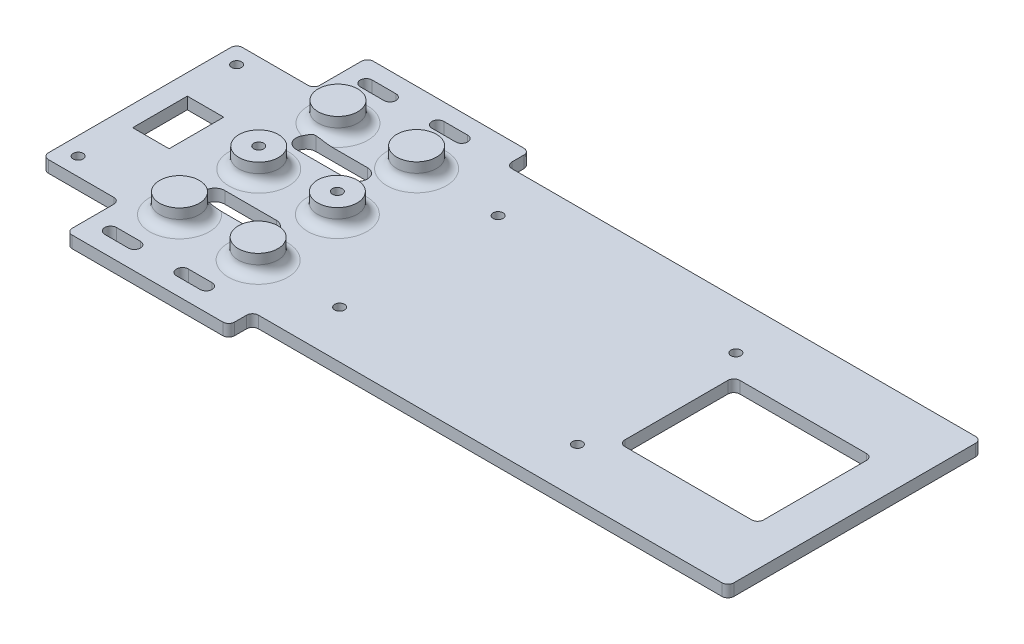
SolidWorks part; units mm, degrees
ref_plane "Front Plane" through (0, 0, 0) normal (0, 0, 1) x (1, 0, 0)
ref_plane "Top Plane" through (0, 0, 0) normal (0, 1, 0) x (1, 0, 0)
ref_plane "Right Plane" through (0, 0, 0) normal (1, 0, 0) x (0, 0, -1)
sketch "Sketch1" plane through (0, 0, 0) normal (0, 1, 0) x (1, 0, 0)
  line L1 (-20.5, -38) -> (20.5, -38)
  line L2 (20.5, -38) -> (20.5, -32)
  line L3 (20.5, -32) -> (140.5, -32)
  line L4 (140.5, -32) -> (140.5, 32)
  line L5 (140.5, 32) -> (20.5, 32)
  line L6 (20.5, 32) -> (20.5, 38)
  line L7 (20.5, 38) -> (-20.5, 38)
  line L8 (-20.5, -24.5) -> (-20.5, -38)
  line L21 (-20.5, 24.5) -> (-20.5, 38)
  line L24 (-40, 24.5) -> (-20.5, 24.5)
  line L26 (-40, 24.5) -> (-40, -24.5)
  line L27 (-40, -24.5) -> (-20.5, -24.5)
  line L28 (-35.5, -20) -> (-35.5, 20) construction
  line L29 (-31, -24.5) -> (-31, 24.5) construction
  circle A0 centre (-35.5, 20) radius 1.25
  circle A1 centre (-35.5, -20) radius 1.25
  point P2 (0, 38)
  point P3 (-40, 0)
  point P22 (-35.5, 0)
  dimension "D7" = 4.5
  dimension "D5" = 4.5
  dimension "D10" = 2.5
  dimension "D1" = 41
  dimension "D2" = 120
  dimension "D3" = 64
  dimension "D4" = 76
  dimension "D6" = 40
  dimension "D8" = 9
  dimension "D9" = 10.5
extrude "Boss-Extrude1" add sketch "Sketch1" along normal blind 3
sketch "Sketch2" plane through (0, 3, 0) normal (0, 1, 0) x (1, 0, 0)
  line L0 (9.925, 0) -> (-9.925, 0) construction
  line L1 (-9.925, 20) -> (-9.925, -20) construction
  line L2 (9.925, 20) -> (9.925, -20) construction
  circle A0 centre (-9.925, 20) radius 5
  circle A1 centre (9.925, 20) radius 5
  circle A2 centre (-9.925, 0) radius 5
  circle A3 centre (9.925, 0) radius 5
  circle A4 centre (9.925, -20) radius 5
  circle A5 centre (-9.925, -20) radius 5
  point P16 (0, 0)
  point P22 (-9.925, 0)
  point P23 (9.925, 0)
  dimension "D2" = 10
  dimension "D1" = 19.85
  dimension "D3" = 40
extrude "Boss-Extrude2" add sketch "Sketch2" along normal blind 5
fillet "Fillet1" radius 2.5 6 edges at (9.925, 3, -15) (-9.925, 3, -15) (9.925, 3, 5) (-9.925, 3, 5) (-9.925, 3, 25) (9.925, 3, 25)
sketch "Sketch3" plane through (0, 0, 0) normal (0, -1, 0) x (-1, 0, 0)
  line L0 (9.925, 0) -> (-9.925, 0) construction
  line L1 (-90.5, 20) -> (-30.5, -20) construction
  line L2 (-30.5, 20) -> (-90.5, -20) construction
  line L4 (9.05, 32.25) -> (15.05, 32.25) construction
  line L5 (9.05, 33.75) -> (15.05, 33.75)
  line L6 (9.05, 30.75) -> (15.05, 30.75)
  line L7 (-9.05, 32.25) -> (-3.05, 32.25) construction
  line L8 (-9.05, 33.75) -> (-3.05, 33.75)
  line L9 (-9.05, 30.75) -> (-3.05, 30.75)
  line L10 (9.05, -32.25) -> (15.05, -32.25) construction
  line L11 (9.05, -30.75) -> (15.05, -30.75)
  line L12 (9.05, -33.75) -> (15.05, -33.75)
  line L13 (-3.05, -32.25) -> (-9.05, -32.25) construction
  line L14 (-3.05, -33.75) -> (-9.05, -33.75)
  line L15 (-3.05, -30.75) -> (-9.05, -30.75)
  line L16 (-9.05, 32.25) -> (9.05, -32.25) construction
  line L17 (20.5, -38) -> (-20.5, -38) construction
  line L18 (3.5, 11.5) -> (-3.5, 11.5) construction
  line L19 (3.5, 9) -> (-3.5, 9)
  line L20 (3.5, 14) -> (-3.5, 14)
  line L21 (3.5, -11.5) -> (-3.5, -11.5) construction
  line L22 (3.5, -14) -> (-3.5, -14)
  line L23 (3.5, -9) -> (-3.5, -9)
  line L24 (0, -11.5) -> (0, 11.5) construction
  line L25 (3.5, -14) -> (9.5, -14)
  line L26 (9.5, -9) -> (3.5, -9)
  line L27 (3.5, 9) -> (9.5, 9)
  line L28 (9.5, 14) -> (3.5, 14)
  line L29 (3.5, -11.5) -> (9.5, -11.5) construction
  line L30 (-20.5, 32) -> (-20.5, 38) construction
  line L31 (25.65, 6.9) -> (34.85, 6.9)
  line L32 (25.65, 6.9) -> (25.65, -6.9)
  line L33 (25.65, -6.9) -> (34.85, -6.9)
  line L34 (34.85, 6.9) -> (34.85, -6.9)
  line L35 (25.65, 6.9) -> (34.85, -6.9) construction
  line L36 (25.65, -6.9) -> (34.85, 6.9) construction
  line L37 (-130.5, 14.5) -> (-95.5, 14.5)
  line L38 (-130.5, 14.5) -> (-130.5, -14.5)
  line L39 (-130.5, -14.5) -> (-95.5, -14.5)
  line L40 (-95.5, 14.5) -> (-95.5, -14.5)
  line L41 (-130.5, 14.5) -> (-95.5, -14.5) construction
  line L42 (-130.5, -14.5) -> (-95.5, 14.5) construction
  line L43 (40, -24.5) -> (20.5, -24.5) construction
  line L45 (-140.5, -32) -> (-140.5, 32) construction
  line L46 (9.05, 32.25) -> (-9.05, -32.25) construction
  circle A2 centre (-30.5, -20) radius 1.25
  circle A3 centre (-90.5, -20) radius 1.25
  circle A4 centre (-30.5, 20) radius 1.25
  circle A5 centre (-90.5, 20) radius 1.25
  arc A6 (9.05, 33.75) -> (9.05, 30.75) centre (9.05, 32.25) ccw
  arc A7 (15.05, 30.75) -> (15.05, 33.75) centre (15.05, 32.25) ccw
  arc A8 (-9.05, 33.75) -> (-9.05, 30.75) centre (-9.05, 32.25) ccw
  arc A9 (-3.05, 30.75) -> (-3.05, 33.75) centre (-3.05, 32.25) ccw
  arc A10 (9.05, -30.75) -> (9.05, -33.75) centre (9.05, -32.25) ccw
  arc A11 (15.05, -33.75) -> (15.05, -30.75) centre (15.05, -32.25) ccw
  arc A12 (-3.05, -33.75) -> (-3.05, -30.75) centre (-3.05, -32.25) ccw
  arc A13 (-9.05, -30.75) -> (-9.05, -33.75) centre (-9.05, -32.25) ccw
  arc A14 (3.5, 9) -> (3.5, 14) centre (3.5, 11.5) ccw
  arc A15 (-3.5, 14) -> (-3.5, 9) centre (-3.5, 11.5) ccw
  arc A16 (3.5, -14) -> (3.5, -9) centre (3.5, -11.5) ccw
  arc A17 (-3.5, -9) -> (-3.5, -14) centre (-3.5, -11.5) ccw
  arc A18 (9.5, -14) -> (9.5, -9) centre (9.5, -11.5) ccw
  arc A19 (9.5, 9) -> (9.5, 14) centre (9.5, 11.5) ccw
  circle A20 centre (-9.925, 0) radius 1.25
  circle A21 centre (9.925, 0) radius 1.25
  point P5 (0, 0)
  point P7 (12.05, 32.25)
  point P8 (0, 0)
  point P16 (-60.5, 0)
  point P17 (-60.5, 0)
  point P26 (-6.05, 32.25)
  point P33 (12.05, -32.25)
  point P40 (-6.05, -32.25)
  point P47 (0, 11.5)
  point P48 (-10.55, 32.25)
  point P49 (-1.55, 32.25)
  point P53 (0, 0)
  point P54 (0, 0)
  point P62 (0, -11.5)
  point P69 (6, -11.5)
  point P70 (-6, -11.5)
  point P75 (0, 0)
  point P89 (30.25, 0)
  point P93 (-29.25, 20)
  point P95 (-113, 0)
  point P102 (30.25, -24.5)
  point P104 (0, 0)
  point P111 (16.55, 32.25)
  dimension "D2" = 2.5
  dimension "D3" = 40
  dimension "D5" = 2.5
  dimension "D9" = 9
  dimension "D4" = 60
  dimension "D6" = 10
  dimension "D7" = 18.1
  dimension "D8" = 3
  dimension "D10" = 5.75
  dimension "D11" = 5
  dimension "D12" = 13.8
  dimension "D13" = 28
  dimension "D14" = 12
  dimension "D15" = 9.2
  dimension "D16" = 19.85
  dimension "D17" = 29
  dimension "D18" = 5
  dimension "D19" = 10
extrude "Cut-Extrude1" cut sketch "Sketch3" against normal through all contours L25 A18 L26 A16 | L23 A17 L22 A16 | L27 A19 L28 A14 | L20 A15 L19 A14 | L12 A11 L11 A10 | L15 A13 L14 A12 | L9 A9 L8 A8 | A4 | A2 | A3 | A5 | A6 L6 A7 L5 | L32 L31 L34 L33 | L38 L37 L40 L39 | A21 | A20
fillet "Fillet2" radius 1.5 16 edges at (140.5, 1.5, -32) (140.5, 1.5, 32) (20.5, 1.5, -32) (20.5, 1.5, 32) (20.5, 1.5, 38) (-20.5, 1.5, 38) (20.5, 1.5, -38) (-40, 1.5, 24.5) (-20.5, 1.5, -24.5) (-20.5, 1.5, 24.5) (-20.5, 1.5, -38) (-40, 1.5, -24.5) (130.5, 1.5, -14.5) (130.5, 1.5, 14.5) (95.5, 1.5, 14.5) (95.5, 1.5, -14.5)
